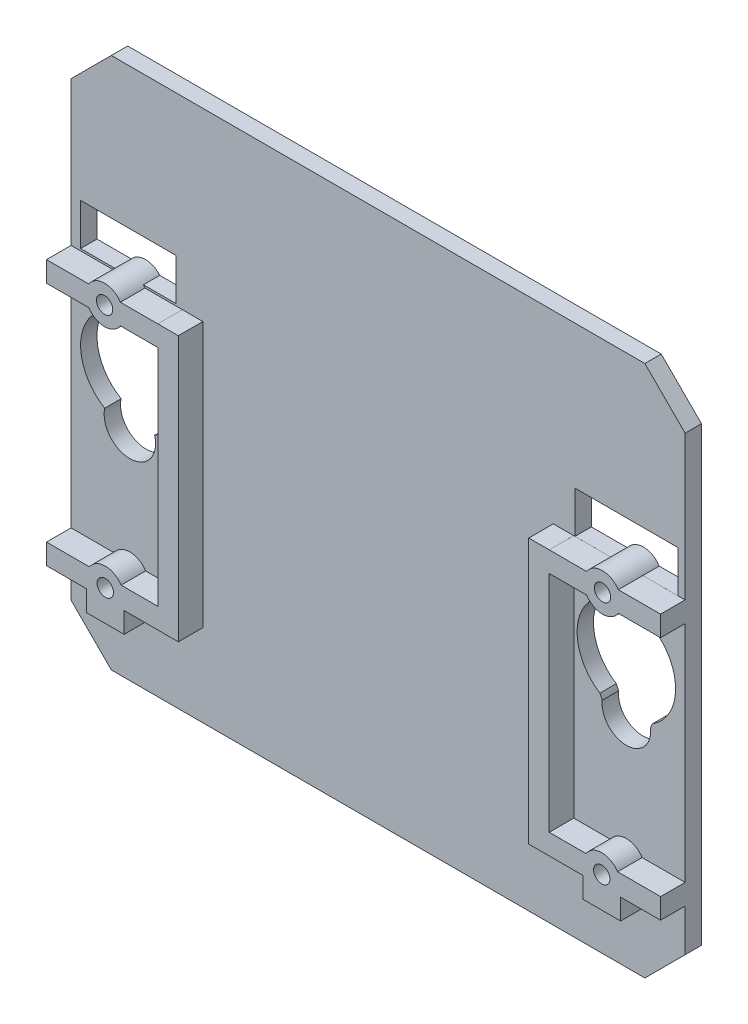
SolidWorks part; units mm, degrees
ref_plane "Front Plane" through (0, 0, 0) normal (0, 0, 1) x (1, 0, 0)
ref_plane "Top Plane" through (0, 0, 0) normal (0, 1, 0) x (1, 0, 0)
ref_plane "Right Plane" through (0, 0, 0) normal (1, 0, 0) x (0, 0, -1)
sketch "Sketch2" plane through (0, 0, 0) normal (0, 0, 1) x (1, 0, 0)
  line L0 (7.0704, 67) -> (62.0787, 67)
  line L1 (5.0821, 0) -> (64.0909, 0)
  line L2 (0.1535, 4.9273) -> (0.1535, 64.0678)
  line L3 (5.0821, 69) -> (64.0909, 69)
  line L4 (69.1535, 5.0681) -> (69.1535, 63.9268)
  line L6 (2.1535, 62.0879) -> (2.1535, 6.9169)
  line L7 (7.0704, 2) -> (62.0787, 2)
  line L8 (67.1535, 61.9216) -> (67.1535, 7.0833)
  line L9 (9.2454, 44.45) -> (9.2454, 43.1985) construction
  line L10 (3.0535, 49.55) -> (15.6035, 49.55)
  line L11 (3.0535, 49.55) -> (3.0535, 44.45)
  line L12 (0, 70.9946) -> (4.9989, 70.9946) construction
  line L13 (3.0535, 44.45) -> (7.3157, 44.45)
  line L14 (15.6035, 49.55) -> (15.6035, 44.45)
  line L15 (18.1456, 44.4709) -> (18.1456, 12.0709)
  line L16 (0.1535, 64.0678) -> (5.0821, 69)
  line L17 (2.1535, 62.0879) -> (7.0704, 67)
  line L19 (10.2504, 13.3209) -> (10.5004, 13.3209)
  line L20 (0.1535, 4.9273) -> (5.0821, 0)
  line L21 (2.1535, 6.9169) -> (7.0704, 2)
  line L22 (15.6456, 44.4709) -> (18.1456, 44.4709)
  line L23 (15.7505, 41.9485) -> (15.7505, 14.5709)
  line L26 (2.1535, 14.5709) -> (7.486, 14.5709)
  line L28 (69.1535, 5.0681) -> (64.0909, 0)
  line L29 (67.1535, 7.0833) -> (62.0787, 2)
  line L30 (64.0909, 69) -> (69.1535, 63.9268)
  line L31 (62.0787, 67) -> (67.1535, 61.9216)
  line L32 (2.0704, 12.0709) -> (7.486, 12.0709)
  line L34 (2.1535, 44.4485) -> (7.3147, 44.4485)
  line L36 (2.0704, 41.9485) -> (7.3147, 41.9485)
  line L38 (8.0835, 11.4734) -> (8.0835, 8.6259)
  line L39 (8.0835, 8.6259) -> (10.5835, 8.6259)
  line L40 (10.5835, 11.4734) -> (10.5835, 8.6259)
  line L41 (11.1811, 14.5709) -> (15.7505, 14.5709)
  line L42 (11.1811, 12.0709) -> (18.1456, 12.0709)
  line L43 (11.1751, 44.45) -> (15.6035, 44.45)
  line L44 (11.1761, 44.4485) -> (17.3391, 44.4485)
  line L45 (11.1761, 41.9485) -> (15.7505, 41.9485)
  circle A0 centre (9.2454, 43.1985) radius 2.3
  arc A1 (12.5614, 29.3869) -> (6.1286, 29.3724) centre (9.3335, 34.4637) ccw
  arc A2 (6.385, 28.7755) -> (12.2823, 28.7732) centre (9.3335, 28.4476) ccw
  arc A3 (12.5614, 29.3869) -> (12.2823, 28.7732) centre (15.2238, 27.8058) ccw
  arc A4 (6.1286, 29.3724) -> (6.385, 28.7755) centre (3.4671, 27.8755) cw
  circle A5 centre (9.2454, 43.1985) radius 1
  circle A6 centre (9.3335, 13.3209) radius 2.2307
  circle A7 centre (9.3335, 13.3209) radius 0.9169
  dimension "D9" = 7.18
  dimension "D11" = 53.6791
  dimension "D12" = 7.18
  dimension "D13" = 6.417
  dimension "D1" = 12.55
  dimension "D2" = 5.1
  dimension "D3" = 2
  dimension "D4" = 2
  dimension "D5" = 2
  dimension "D6" = 0.9
  dimension "D7" = 17.45
  dimension "D8" = 1.2515
  dimension "D10" = 32.5363
  dimension "D14" = 2.5
  dimension "D15" = 2.5
  dimension "D16" = 1.25
  dimension "D18" = 1.25
  dimension "D19" = 1.25
extrude "Boss-Extrude3" add sketch "Sketch2" along normal blind 2
sketch "Sketch7" plane through (0, 0, 2) normal (0, 0, 1) x (1, 0, 0)
  line L0 (2.1535, 62.0879) -> (2.1535, 6.9169) construction
  line L1 (7.0704, 67) -> (62.0787, 67) construction
  line L2 (11.2642, 14.57) -> (18.2535, 14.57)
  line L3 (15.7535, 44.45) -> (18.2535, 44.45)
  line L4 (15.7535, 44.45) -> (15.7535, 44.4485)
  line L6 (18.2535, 44.45) -> (18.2535, 16.5346)
  line L7 (2.1535, 44.4485) -> (7.3147, 44.4485)
  line L8 (2.1535, 44.4485) -> (2.1535, 41.9485)
  line L9 (2.1535, 41.9485) -> (7.3147, 41.9485)
  line L11 (2.1535, 14.57) -> (7.4028, 14.57)
  line L12 (2.1535, 14.57) -> (2.1535, 12.07)
  line L13 (2.1535, 12.07) -> (7.4028, 12.07)
  line L14 (18.2535, 14.57) -> (18.2535, 12.07)
  line L16 (15.7535, 16.5346) -> (15.7535, 12.07)
  line L17 (15.7535, 12.07) -> (18.2535, 12.07)
  line L18 (18.2535, 16.5346) -> (18.2535, 12.07)
  line L20 (7.0335, 12.07) -> (7.0335, 9.5478)
  line L21 (7.0335, 9.5478) -> (11.6335, 9.5478)
  line L22 (11.6335, 12.07) -> (11.6335, 9.5478)
  line L23 (11.2642, 12.07) -> (18.2535, 12.07)
  line L24 (15.7535, 41.9485) -> (15.7535, 16.5346)
  line L25 (11.1761, 44.4485) -> (17.3319, 44.4485)
  line L26 (11.1761, 41.9485) -> (15.7535, 41.9485)
  arc A0 (7.3157, 44.45) -> (7.3147, 44.4485) centre (9.2454, 43.1985) ccw
  arc A1 (11.1751, 44.45) -> (7.3157, 44.45) centre (9.2454, 43.1985) ccw construction
  circle A2 centre (9.2454, 43.1985) radius 1
  arc A3 (11.2642, 14.57) -> (7.4028, 14.57) centre (9.3335, 13.32) ccw
  circle A4 centre (9.3335, 13.32) radius 1
  arc A5 (3.3174, 34.4637) -> (9.3199, 40.4798) centre (9.3335, 34.4637) ccw
  arc A6 (12.5614, 29.3869) -> (6.1286, 29.3724) centre (9.3335, 34.4637) ccw construction
  arc A7 (7.3147, 41.9485) -> (11.1761, 41.9485) centre (9.2454, 43.1985) ccw
  arc A8 (11.1761, 44.4485) -> (9.2454, 45.4985) centre (9.2454, 43.1985) ccw
  arc A9 (7.4028, 12.07) -> (11.2642, 12.07) centre (9.3335, 13.32) ccw
  dimension "D1" = 7.18
  dimension "D3" = 6.42
  dimension "D2" = 53.68
  dimension "D4" = 2.5
  dimension "D6" = 1.25
  dimension "D7" = 2.5
  dimension "D8" = 1.25
extrude "Boss-Extrude5" add sketch "Sketch7" along normal blind 3
ref_plane "Plane1" through (34.6535, 0, 0) normal (-1, 0, 0) x (0, 0, 1)
sketch "Sketch15" plane through (0, 0, 2) normal (0, 0, 1) x (1, 0, 0)
  circle A0 centre (9.3335, 34.4637) radius 6.0161
  circle A1 centre (9.3335, 28.4476) radius 2.9667
mirror "Mirror4" about plane through (34.6535, 0, 0) normal (-1, 0, 0) of "Boss-Extrude3", "Boss-Extrude5"
extrude "Cut-Extrude5" cut sketch "Sketch15" against normal blind 3 contours A1 | A0
sketch "Sketch21" plane through (0, 0, 2) normal (0, 0, 1) x (1, 0, 0)
  line L0 (3.3174, 34.4637) -> (3.3174, 54.9397) construction
  line L1 (15.3496, 34.4637) -> (15.3496, 54.9397) construction
  line L2 (3.3174, 44.7017) -> (7.5046, 44.7017)
  line L3 (10.9861, 44.7017) -> (15.3496, 44.7017)
  line L4 (15.3496, 44.7017) -> (15.3496, 49.7017)
  line L5 (15.3496, 49.7017) -> (3.3174, 49.7017)
  line L6 (3.3174, 49.7017) -> (3.3174, 44.7017)
  arc A0 (12.2086, 29.1791) -> (6.4584, 29.1791) centre (9.3335, 34.4637) ccw construction
  arc A1 (11.1761, 44.4485) -> (7.3147, 44.4485) centre (9.2454, 43.1985) ccw construction
  arc A2 (7.5046, 44.7017) -> (10.9861, 44.7017) centre (9.2454, 43.1985) cw
  dimension "D1" = 5
extrude "Cut-Extrude6" cut sketch "Sketch21" against normal blind 3 contours L2 A2 L3 L4 L5 L6
sketch "Sketch29" plane through (0, 0, 2) normal (0, 0, 1) x (1, 0, 0)
  line L0 (3.3174, 34.4637) -> (3.3174, 55.1273) construction
  line L1 (15.3496, 34.4637) -> (15.3496, 55.1273) construction
  line L2 (3.3174, 44.7955) -> (7.5902, 44.7955)
  line L3 (10.9005, 44.7955) -> (15.3496, 44.7955)
  line L4 (15.3496, 44.7955) -> (15.3496, 49.7955)
  line L5 (15.3496, 49.7955) -> (3.3174, 49.7955)
  line L6 (3.3174, 49.7955) -> (3.3174, 44.7955)
  arc A0 (12.2086, 29.1791) -> (6.4584, 29.1791) centre (9.3335, 34.4637) ccw construction
  arc A1 (11.1761, 44.4485) -> (10.9861, 44.7017) centre (9.2454, 43.1985) ccw construction
  arc A2 (11.1761, 44.4485) -> (7.3147, 44.4485) centre (9.2454, 43.1985) ccw construction
  arc A3 (10.9005, 44.7955) -> (7.5902, 44.7955) centre (9.2454, 43.1985) ccw
  dimension "D1" = 5
extrude "Cut-Extrude7" cut sketch "Sketch29" against normal blind 10
mirror "Mirror9" about plane through (34.6535, 0, 0) normal (-1, 0, 0) of "Cut-Extrude7"
mirror "Mirror5" about plane through (34.6535, 0, 0) normal (-1, 0, 0) of "Cut-Extrude5"
other "SurfaceCut1"
sketch "Sketch30" plane through (34.6535, 0, 0) normal (1, 0, 0) x (0, 0, -1)
  line L1 (-2, 67) -> (0, 67)
  line L2 (-2, 67) -> (-2, 2)
  line L3 (-2, 2) -> (0, 2)
  line L4 (0, 67) -> (0, 2)
extrude "Boss-Extrude6" add sketch "Sketch30" along normal blind 5 contours L2 L1 L4 L3
ref_plane "Plane2" through (39.6535, 0, 0) normal (1, 0, 0) x (0, 0, -1)
mirror "Mirror12" about plane through (39.6535, 0, 0) normal (1, 0, 0) of "Boss-Extrude5", "Boss-Extrude3"
sketch "Sketch31" plane through (0, 0, 2) normal (0, 0, 1) x (1, 0, 0)
  circle A0 centre (9.3335, 34.4637) radius 5.8428
  circle A1 centre (9.3335, 28.6209) radius 3.14
extrude "Cut-Extrude8" cut sketch "Sketch31" against normal blind 5 contours A1 A0 | A0 A1 | A0 A1
sketch "Sketch33" plane through (0, 0, 2) normal (0, 0, 1) x (1, 0, 0)
  line L0 (15.1751, 34.5818) -> (14.7789, 54.1844) construction
  line L1 (12.1535, 49.7955) -> (12.1535, 44.7017) construction
  line L2 (12.1535, 49.7955) -> (14.9706, 49.7955)
  line L3 (12.1535, 49.7955) -> (12.1535, 44.7017)
  line L4 (12.1535, 44.7017) -> (14.9706, 44.7017)
  line L5 (14.9706, 49.7955) -> (14.9706, 44.7017)
  arc A0 (12.358, 29.4647) -> (12.1535, 39.581) centre (9.3335, 34.4637) ccw construction
extrude "Cut-Extrude9" cut sketch "Sketch33" against normal blind 5
sketch "Sketch35" plane through (0, 0, 2) normal (0, 0, 1) x (1, 0, 0)
  line L0 (2.1535, 62.0879) -> (7.0704, 67) construction
  line L1 (6.242, 0) -> (73.0651, 0)
  line L2 (0, 6.242) -> (0, 62.7635)
  line L3 (6.2425, 69) -> (73.0645, 69)
  line L4 (79.1535, 6.0884) -> (79.1535, 62.9169)
  line L5 (77.1535, 62.0879) -> (77.1535, 44.4485) construction
  line L6 (7.0704, 67) -> (72.2366, 67) construction
  line L7 (6.2425, 69) -> (0, 62.7635)
  line L8 (0, 6.242) -> (6.242, 0)
  line L9 (2.1535, 6.9169) -> (7.0704, 2) construction
  line L10 (73.0645, 69) -> (79.1535, 62.9169)
  line L11 (77.1535, 62.0879) -> (72.2366, 67) construction
  line L12 (73.0651, 0) -> (79.1535, 6.0884)
  line L13 (77.1535, 6.9169) -> (72.2366, 2) construction
  line L14 (7.0704, 67) -> (72.2366, 67)
  line L15 (72.2366, 67) -> (77.1535, 62.0879)
  line L16 (77.1535, 62.0879) -> (77.1535, 6.9169)
  line L17 (77.1535, 6.9169) -> (72.2366, 2)
  line L18 (72.2366, 2) -> (7.0704, 2)
  line L19 (7.0704, 2) -> (2.1535, 6.9169)
  line L20 (2.1535, 6.9169) -> (2.1535, 62.0879)
  point P13 (4.6119, 64.5439)
  point P26 (74.6951, 4.4584)
  dimension "D1" = 2
  dimension "D2" = 2
  dimension "D3" = 2
  dimension "D4" = 2
  dimension "D5" = 2
  dimension "D6" = 2
